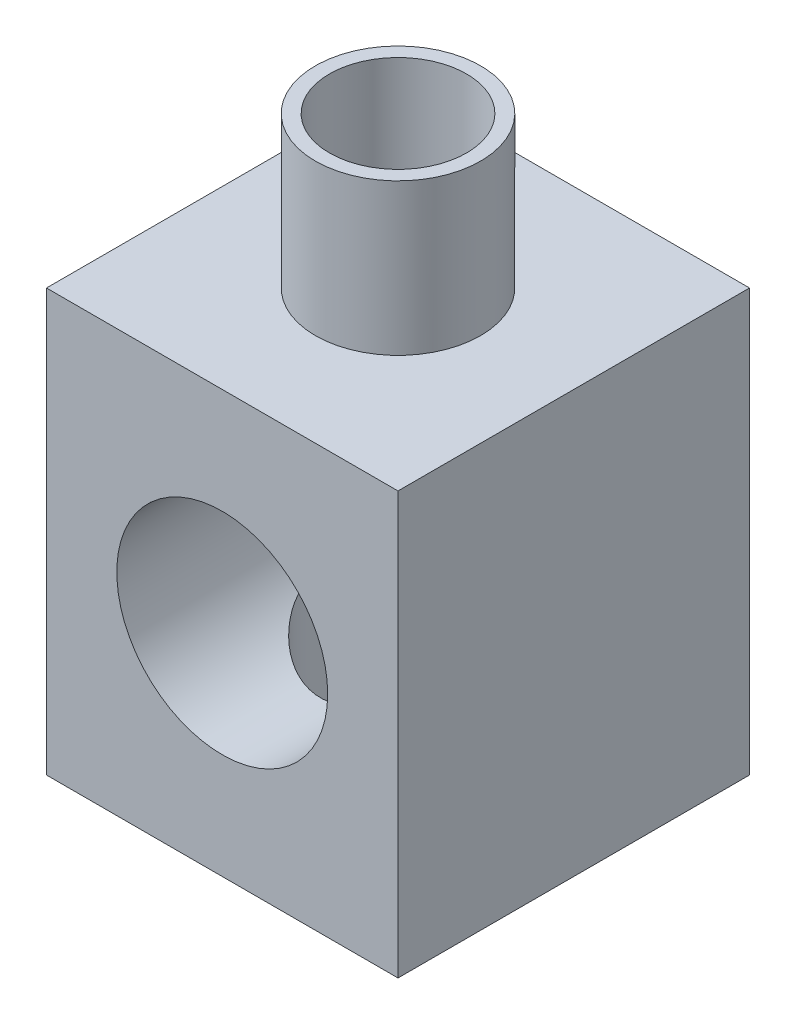
SolidWorks part; units mm, degrees
ref_plane "Alzado" through (0, 0, 0) normal (0, 0, 1) x (1, 0, 0)
ref_plane "Planta" through (0, 0, 0) normal (0, 1, 0) x (1, 0, 0)
ref_plane "Vista lateral" through (0, 0, 0) normal (1, 0, 0) x (0, 0, -1)
sketch "Croquis1" plane through (0, 0, 0) normal (0, 1, 0) x (1, 0, 0)
  line L1 (-25, -25) -> (25, -25)
  line L2 (-25, -25) -> (-25, 25)
  line L3 (-25, 25) -> (25, 25)
  line L4 (25, -25) -> (25, 25)
  line L5 (-25, -25) -> (25, 25) construction
  line L6 (-25, 25) -> (25, -25) construction
  circle A0 centre (0, 0) radius 11
  dimension "D1" = 22
  dimension "D2" = 50
  dimension "D3" = 50
extrude "Saliente-Extruir1" add sketch "Croquis1" along normal blind 60
sketch "Croquis3" plane through (0, 0, 25) normal (0, 0, 1) x (1, 0, 0)
  line L0 (0, 60) -> (0, 0) construction
  line L1 (-25, 60) -> (25, 60) construction
  circle A0 centre (0, 30) radius 15
  dimension "D1" = 30
extrude "Cortar-Extruir1" cut sketch "Croquis3" against normal blind 47
sketch "Croquis4" plane through (0, 0, -22) normal (0, 0, 1) x (1, 0, 0)
  circle A0 centre (0, 30) radius 4
  dimension "D1" = 8
extrude "Cortar-Extruir2" cut sketch "Croquis4" against normal blind 10
sketch "Croquis5" plane through (0, 60, 0) normal (0, 1, 0) x (1, 0, 0)
  circle A0 centre (0, 0) radius 9.75
  circle A1 centre (0, 0) radius 11.75
  dimension "D1" = 23.5
  dimension "D2" = 2
extrude "Saliente-Extruir3" add sketch "Croquis5" along normal blind 21.5 and the other way blind 5
sketch "Croquis7" plane through (0, 0, 0) normal (0, -1, 0) x (1, 0, 0)
  circle A0 centre (0, 0) radius 11
  circle A1 centre (0, 0) radius 13
  dimension "D1" = 22
  dimension "D2" = 2
extrude "Saliente-Extruir4" add sketch "Croquis7" along normal blind 10
